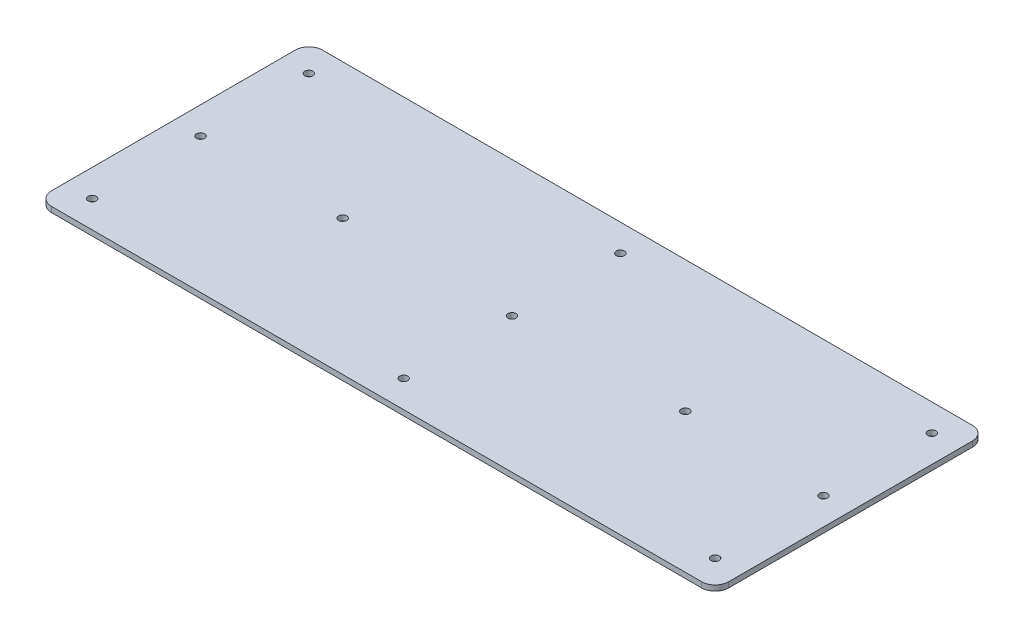
SolidWorks part; units mm, degrees
ref_plane "Front Plane" through (0, 0, 0) normal (0, 0, 1) x (1, 0, 0)
ref_plane "Top Plane" through (0, 0, 0) normal (0, 1, 0) x (1, 0, 0)
ref_plane "Right Plane" through (0, 0, 0) normal (1, 0, 0) x (0, 0, -1)
sketch "Sketch1" plane through (0, 0, 0) normal (0, 1, 0) x (1, 0, 0)
  line L1 (-120, 50) -> (120, 50)
  line L2 (-125, 45) -> (-125, -45)
  line L3 (-120, -50) -> (120, -50)
  line L4 (125, 45) -> (125, -45)
  line L5 (-125, 50) -> (125, -50) construction
  line L6 (-125, -50) -> (125, 50) construction
  circle A0 centre (0, 40) radius 1.5
  circle A1 centre (-115, 40) radius 1.5
  circle A2 centre (115, 40) radius 1.5
  circle A3 centre (-115, 0) radius 1.5
  circle A4 centre (-115, -40) radius 1.5
  circle A5 centre (0, -40) radius 1.5
  circle A6 centre (115, -40) radius 1.5
  circle A7 centre (0, 0) radius 1.5
  circle A8 centre (115, 0) radius 1.5
  arc A9 (125, 45) -> (120, 50) centre (120, 45) ccw
  arc A10 (125, -45) -> (120, -50) centre (120, -45) cw
  arc A11 (-120, -50) -> (-125, -45) centre (-120, -45) cw
  arc A12 (-125, 45) -> (-120, 50) centre (-120, 45) cw
  circle A13 centre (-62.5, 0) radius 1.5
  circle A14 centre (62.5, 1.5) radius 1.5
  point P0 (0, 0)
  dimension "D3" = 10
  dimension "D4" = 10
  dimension "D5" = 10
  dimension "D6" = 10
  dimension "D7" = 10
  dimension "D9" = 10
  dimension "D10" = 10
  dimension "D11" = 10
  dimension "D12" = 10
  dimension "D13" = 10
  dimension "D14" = 3
  dimension "D15" = 3
  dimension "D16" = 5
  dimension "D17" = 62.5
  dimension "D19" = 10
  dimension "D20" = 125
  dimension "D21" = 125
  dimension "D1" = 100
  dimension "D2" = 250
  dimension "D8" = 10
  dimension "D18" = 62.5
extrude "Boss-Extrude1" add sketch "Sketch1" along normal blind 2
